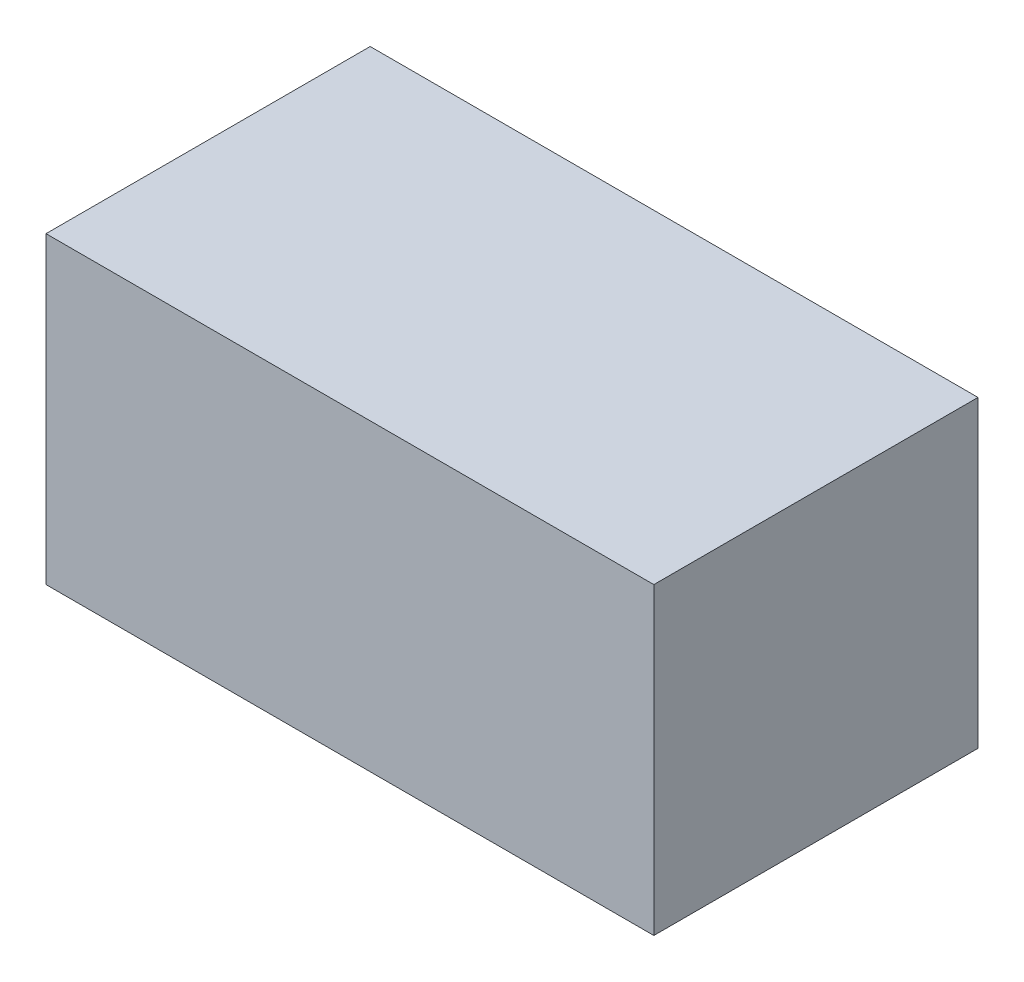
SolidWorks part; units mm, degrees
ref_plane "Front Plane" through (0, 0, 0) normal (0, 0, 1) x (1, 0, 0)
ref_plane "Top Plane" through (0, 0, 0) normal (0, 1, 0) x (1, 0, 0)
ref_plane "Right Plane" through (0, 0, 0) normal (1, 0, 0) x (0, 0, -1)
sketch "Sketch1" plane through (0, 0, 0) normal (0, 1, 0) x (1, 0, 0)
  line L1 (0, 0) -> (-180, 0)
  line L2 (0, 0) -> (0, 96)
  line L3 (0, 96) -> (-180, 96)
  line L4 (-180, 0) -> (-180, 96)
  dimension "D1" = 180
  dimension "D2" = 96
extrude "Extrude1" add sketch "Sketch1" along normal blind 90
